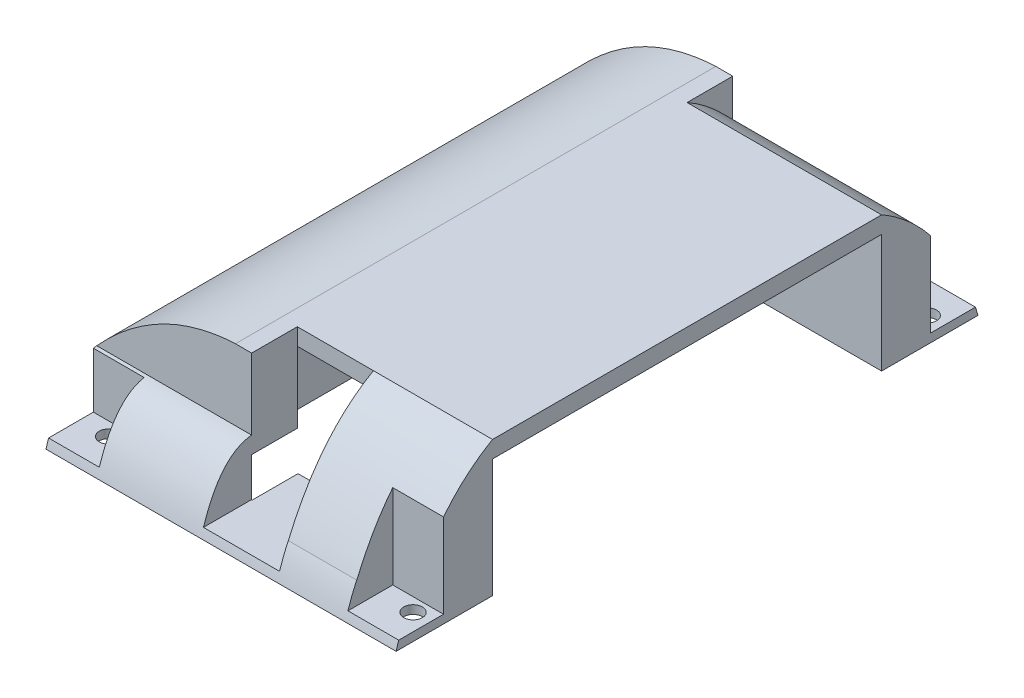
SolidWorks part; units mm, degrees
ref_plane "Front Plane" through (0, 0, 0) normal (0, 0, 1) x (1, 0, 0)
ref_plane "Top Plane" through (0, 0, 0) normal (0, 1, 0) x (1, 0, 0)
ref_plane "Right Plane" through (0, 0, 0) normal (1, 0, 0) x (0, 0, -1)
sketch "Sketch1" plane through (0, 0, 0) normal (0, 1, 0) x (1, 0, 0)
  line L1 (-11.684, -36.068) -> (11.684, -36.068)
  line L2 (-11.684, -36.068) -> (-11.684, 36.068)
  line L3 (-11.684, 36.068) -> (11.684, 36.068)
  line L4 (11.684, -36.068) -> (11.684, 36.068)
  line L5 (-11.684, -36.068) -> (11.684, 36.068) construction
  line L6 (-11.684, 36.068) -> (11.684, -36.068) construction
  point P0 (0, 0)
  dimension "D1" = 23.368
  dimension "D2" = 72.136
extrude "Boss-Extrude1" add sketch "Sketch1" along normal blind 2.54
sketch "Sketch2" plane through (0, 2.54, 0) normal (0, 1, 0) x (1, 0, 0)
  line L1 (11.684, -29.21) -> (9.144, -29.21)
  line L2 (11.684, -29.21) -> (11.684, 29.21)
  line L3 (11.684, 29.21) -> (9.144, 29.21)
  line L4 (9.144, -29.21) -> (9.144, 29.21)
  dimension "D1" = 58.42
  dimension "D2" = 2.54
extrude "Cut-Extrude1" cut sketch "Sketch2" against normal blind 2.54
sketch "Sketch3" plane through (0, 2.54, 0) normal (0, 1, 0) x (1, 0, 0)
  line L1 (11.684, -36.068) -> (9.144, -36.068)
  line L2 (11.684, -36.068) -> (11.684, -29.21)
  line L3 (11.684, -29.21) -> (9.144, -29.21)
  line L4 (9.144, -36.068) -> (9.144, -29.21)
  line L5 (11.684, 36.068) -> (9.144, 36.068)
  line L6 (11.684, 36.068) -> (11.684, 29.21)
  line L7 (11.684, 29.21) -> (9.144, 29.21)
  line L8 (9.144, 36.068) -> (9.144, 29.21)
extrude "Boss-Extrude2" add sketch "Sketch3" along normal blind 8.128
sketch "Sketch4" plane through (0, 10.668, 0) normal (0, 1, 0) x (1, 0, 0)
  line L1 (9.144, -29.21) -> (40.894, -29.21)
  line L2 (9.144, -29.21) -> (9.144, 29.21)
  line L3 (9.144, 29.21) -> (40.894, 29.21)
  line L4 (40.894, -29.21) -> (40.894, 29.21)
  dimension "D1" = 31.75
extrude "Boss-Extrude3" add sketch "Sketch4" along normal blind 2.54 separate body
sketch "Sketch5" plane through (0, 10.668, 0) normal (0, 1, 0) x (1, 0, 0)
  line L1 (11.684, -36.068) -> (9.144, -36.068)
  line L2 (11.684, -36.068) -> (11.684, -29.21)
  line L3 (11.684, -29.21) -> (9.144, -29.21)
  line L4 (9.144, -36.068) -> (9.144, -29.21)
  line L5 (9.144, 36.068) -> (11.684, 36.068)
  line L6 (9.144, 36.068) -> (9.144, 29.21)
  line L7 (9.144, 29.21) -> (11.684, 29.21)
  line L8 (11.684, 36.068) -> (11.684, 29.21)
extrude "Boss-Extrude4" add sketch "Sketch5" along normal blind 2.54
sketch "Sketch6" plane through (0, 0, 0) normal (1, 0, 0) x (0, 0, -1)
  line L0 (36.068, 2.54) -> (36.068, -7.112)
  line L1 (36.068, -7.112) -> (43.688, -7.112)
  line L2 (28.9179, 0) -> (-28.9179, 0) construction
  line L3 (29.21, 0) -> (29.21, 2.54) construction
  spline S0 degree 2 poles (43.688, -7.112) (39.5681, 7.5456) (29.21, 0) knots 0 0 0 1 1 1
  dimension "D1" = 7.62
extrude "Boss-Extrude5" add sketch "Sketch6" along normal up to surface (40.894 mm away) and the other way up to surface (11.684 mm away) contours L1 S0 L0 up to face at (40.894, 11.938, 0) other way up to face at (-11.684, 1.27, 0)
sketch "Sketch7" plane through (11.684, 0, 0) normal (1, 0, 0) x (0, 0, -1)
  line L0 (29.21, 13.208) -> (29.21, -7.112)
  line L1 (29.21, -7.112) -> (43.688, -7.112)
  spline S0 degree 2 poles (43.688, -7.112) (33.2102, 25.1026) (0, 13.208) knots 0 0 0 1 1 1
extrude "Boss-Extrude6" add sketch "Sketch7" along normal up to surface (29.21 mm away) contours S0 M2 M4 M5 M6 M12 | L1 S0 L0 M2 M12 M6 up to face at (40.894, 11.938, 0)
ref_plane "Plane1" through (0, 25.4, 0) normal (0, 1, 0) x (1, 0, 0)
sketch "Sketch10" plane through (0, 25.4, 0) normal (0, 1, 0) x (1, 0, 0)
  line L10 (-11.684, 43.688) -> (-4.064, 43.688)
  line L11 (-11.684, 43.688) -> (-11.684, 36.576)
  line L12 (-11.684, 36.576) -> (-4.064, 36.576)
  line L13 (-4.064, 43.688) -> (-4.064, 36.576)
  line L14 (40.894, 43.688) -> (33.274, 43.688)
  line L15 (40.894, 43.688) -> (40.894, 36.576)
  line L16 (40.894, 36.576) -> (33.274, 36.576)
  line L17 (33.274, 43.688) -> (33.274, 36.576)
  dimension "D1" = 7.112
  dimension "D2" = 7.62
  dimension "D3" = 7.62
  dimension "D4" = 7.112
extrude "Cut-Extrude2" cut sketch "Sketch10" against normal blind 31.242 contours L13 L10 L11 L12 | L14 L17 L16 L15
sketch "Sketch12" plane through (0, -7.112, 0) normal (0, -1, 0) x (1, 0, 0)
  circle A0 centre (-7.366, -38.608) radius 1.397
  circle A1 centre (38.354, -38.608) radius 1.397
extrude "Cut-Extrude3" cut sketch "Sketch12" against normal through all contours A0 | A1
mirror "Mirror1" about plane through (0, 0, 0) normal (0, 0, 1) of "Cut-Extrude3", "Cut-Extrude2", "Boss-Extrude6", "Boss-Extrude5"
sketch "Sketch13" plane through (0, 0, 36.068) normal (0, 0, 1) x (1, 0, 0)
  line L0 (9.144, 13.208) -> (9.144, 2.54)
  line L1 (9.144, 2.54) -> (-11.684, 2.54)
  line L2 (-11.684, 2.54) -> (9.144, 2.54) construction
  spline S0 degree 2 poles (-11.684, 2.54) (-1.4262, 13.787) (11.684, 13.208) knots 0 0 0 1 1 1
extrude "Boss-Extrude7" add sketch "Sketch13" against normal up to surface (72.136 mm away) contours S0 L1 M5 up to face at (10.668, 7.7862, -36.068)
sketch "Sketch14" plane through (0, 25.4, 0) normal (0, 1, 0) x (1, 0, 0)
  line L1 (1.016, 36.068) -> (9.144, 36.068)
  line L2 (1.016, 36.068) -> (1.016, 43.688)
  line L3 (1.016, 43.688) -> (9.144, 43.688)
  line L4 (9.144, 36.068) -> (9.144, 43.688)
  line L5 (11.5744, -43.688) -> (23.0044, -43.688)
  line L6 (11.5744, -43.688) -> (11.5744, -29.21)
  line L7 (11.5744, -29.21) -> (23.0044, -29.21)
  line L8 (23.0044, -43.688) -> (23.0044, -29.21)
  dimension "D1" = 8.128
  dimension "D2" = 7.62
  dimension "D3" = 11.43
  dimension "D4" = 14.478
extrude "Cut-Extrude4" cut sketch "Sketch14" against normal blind 31.242
